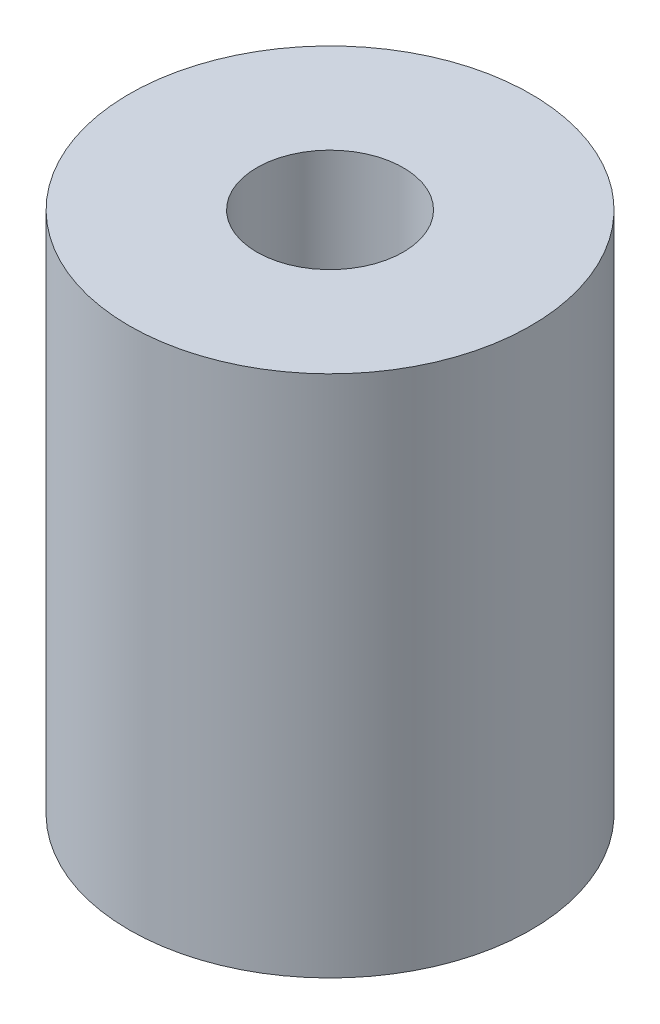
SolidWorks part; units mm, degrees
material "Copper"
ref_plane "Front Plane" through (0, 0, 0) normal (0, 0, 1) x (1, 0, 0)
ref_plane "Top Plane" through (0, 0, 0) normal (0, 1, 0) x (1, 0, 0)
ref_plane "Right Plane" through (0, 0, 0) normal (1, 0, 0) x (0, 0, -1)
sketch "Sketch1" plane through (0, 0, 0) normal (0, 1, 0) x (1, 0, 0)
  circle A0 centre (0, 0) radius 11.1125
  circle A1 centre (0, 0) radius 4.0513
  dimension "D1" = 8.1026
  dimension "D2" = 22.225
extrude "Boss-Extrude1" add sketch "Sketch1" along normal blind 28.956
